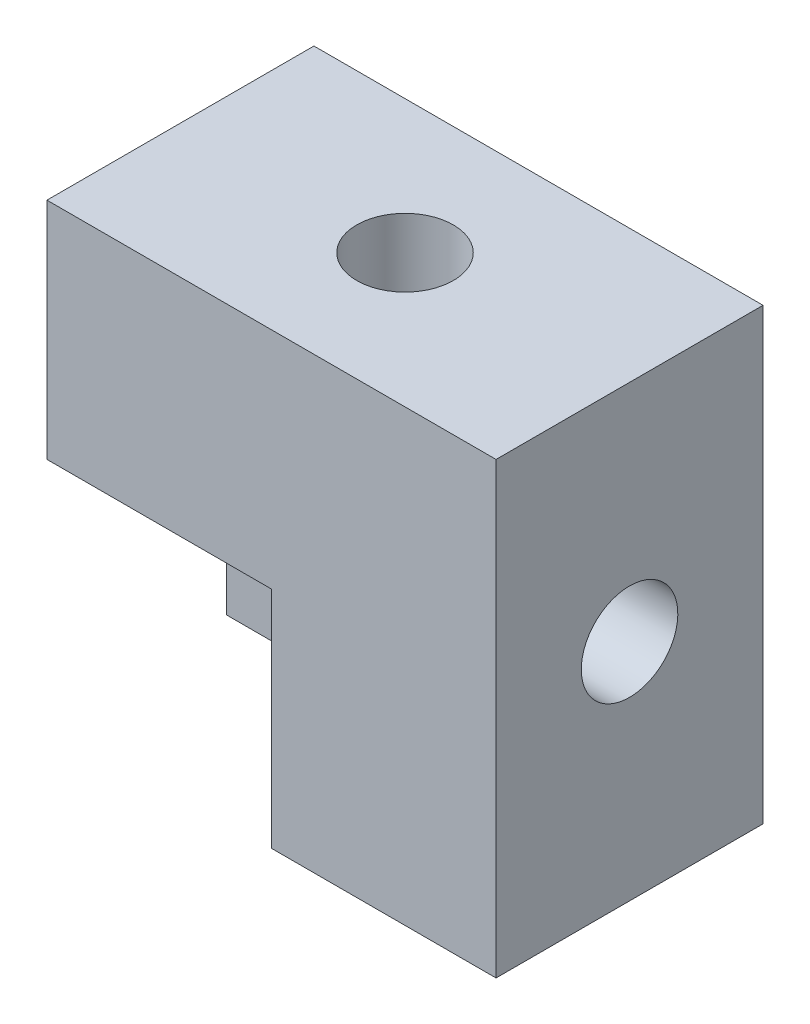
SolidWorks part; units mm, degrees
ref_plane "Front Plane" through (0, 0, 0) normal (0, 0, 1) x (1, 0, 0)
ref_plane "Top Plane" through (0, 0, 0) normal (0, 1, 0) x (1, 0, 0)
ref_plane "Right Plane" through (0, 0, 0) normal (1, 0, 0) x (0, 0, -1)
sketch "Sketch1" plane through (0, 0, 0) normal (0, 0, 1) x (1, 0, 0)
  line L0 (0, 0) -> (20, 0)
  line L1 (20, 0) -> (20, 20)
  line L2 (20, 20) -> (0, 20)
  line L3 (0, 20) -> (0, 0)
  dimension "D1" = 20
  dimension "D2" = 20
extrude "Boss-Extrude1" add sketch "Sketch1" along normal blind 11.89 contours L2 L3 L0 L1
sketch "Sketch2" plane through (0, 0, 11.89) normal (0, 0, 1) x (1, 0, 0)
  line L1 (0, 0) -> (10, 0)
  line L2 (0, 0) -> (0, 10)
  line L3 (0, 10) -> (10, 10)
  line L4 (10, 0) -> (10, 10)
  dimension "D1" = 10
  dimension "D2" = 10
extrude "Cut-Extrude1" cut sketch "Sketch2" against normal blind 8
sketch "Sketch99" plane through (0, 0, 0) normal (0, 0, -1) x (-1, 0, 0)
  line L0 (-10, 20) -> (-10, 0) construction
  line L1 (-20, 20) -> (0, 20) construction
  line L2 (0, 0) -> (-20, 0) construction
  line L3 (-20, 10) -> (-10, 10) construction
  line L4 (-20, 0) -> (-20, 20) construction
  line L6 (-15, 10) -> (-15, 20) construction
  line L7 (-15, 15) -> (-20, 15) construction
  circle A1 centre (-15, 15) radius 2.15
  dimension "D1" = 4.3
sketch "Sketch100" plane through (20, 0, 0) normal (1, 0, 0) x (0, 0, -1)
  line L0 (-5.945, 20) -> (-5.945, 0) construction
  line L1 (-11.89, 20) -> (0, 20) construction
  line L2 (-11.89, 0) -> (0, 0) construction
  line L3 (-11.89, 10) -> (-5.945, 10) construction
  line L4 (-11.89, 0) -> (-11.89, 20) construction
  circle A0 centre (-5.945, 10) radius 2.15
  dimension "D1" = 4.3
sketch "Sketch101" plane through (0, 20, 0) normal (0, 1, 0) x (1, 0, 0)
  line L0 (10, -11.89) -> (10, 0) construction
  line L1 (20, -11.89) -> (0, -11.89) construction
  line L2 (20, 0) -> (0, 0) construction
  line L3 (0, -5.945) -> (10, -5.945) construction
  line L4 (0, -11.89) -> (0, 0) construction
  circle A0 centre (10, -5.945) radius 2.15
  dimension "D1" = 4.3
extrude "Cut-Extrude92" cut sketch "Sketch101" against normal blind 6.825
extrude "Cut-Extrude93" cut sketch "Sketch100" against normal blind 6.875
extrude "Cut-Extrude94" cut sketch "Sketch99" against normal blind 4.825
